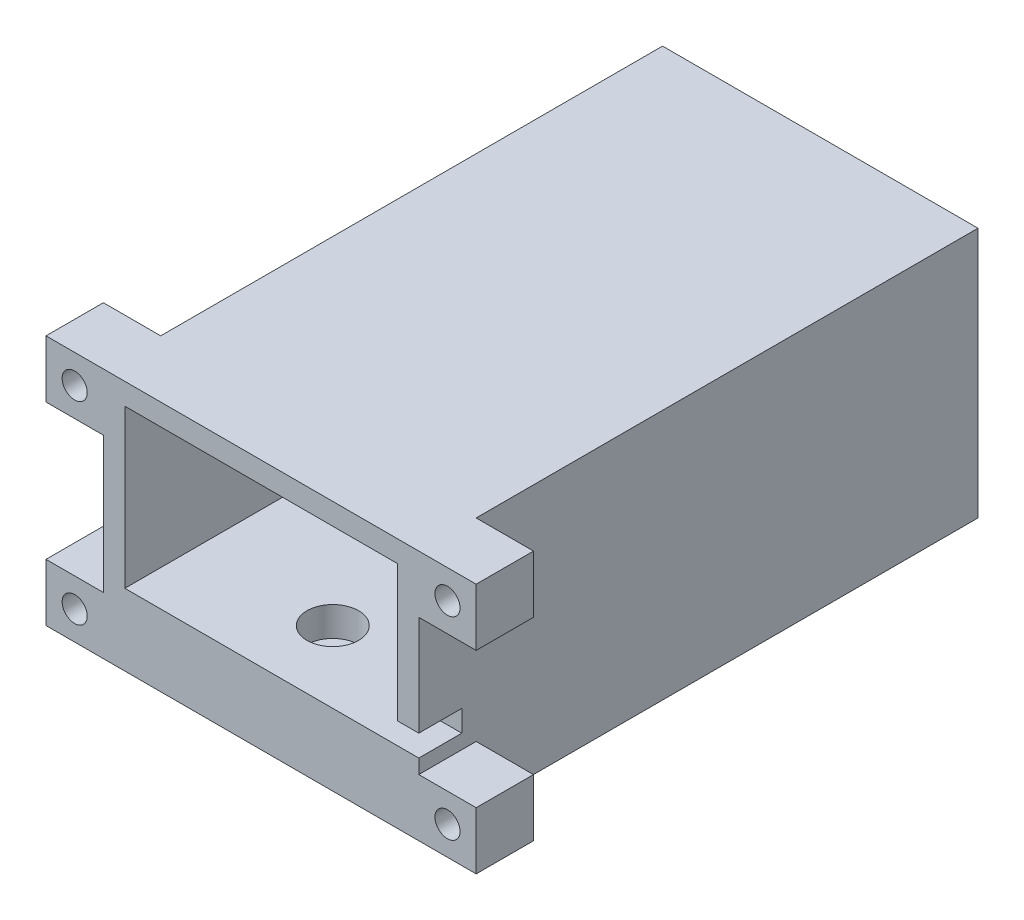
SolidWorks part; units mm, degrees
ref_plane "前基準面" through (0, 0, 0) normal (0, 0, 1) x (1, 0, 0)
ref_plane "上基準面" through (0, 0, 0) normal (0, 1, 0) x (1, 0, 0)
ref_plane "右基準面" through (0, 0, 0) normal (1, 0, 0) x (0, 0, -1)
sketch "草圖1" plane through (0, 0, 0) normal (0, 1, 0) x (1, 0, 0)
  line L1 (-22, 39) -> (22, 39)
  line L2 (-22, 39) -> (-22, -39)
  line L3 (-22, -39) -> (22, -39)
  line L4 (22, 39) -> (22, -39)
  line L5 (-22, 39) -> (22, -39) construction
  line L6 (-22, -39) -> (22, 39) construction
  point P0 (0, 0)
  dimension "D1" = 78
  dimension "D2" = 44
extrude "填料-伸長1" add sketch "草圖1" along normal blind 35
shell "薄殼1" thickness 3
sketch "草圖3" plane through (0, 10, 0) normal (0, 1, 0) x (1, 0, 0)
  line L0 (-22, -39) -> (22, -39) construction
  circle A0 centre (0, 25) radius 3.6
  circle A1 centre (0, -29) radius 3.6
  dimension "D1" = 7.2
  dimension "D2" = 54
  dimension "D3" = 10
extrude "除料-伸長1" cut sketch "草圖3" against normal blind 4.1
sketch "草圖4" plane through (0, 10, 0) normal (0, 1, 0) x (1, 0, 0)
  circle A0 centre (0, 25) radius 2.25
  circle A1 centre (0, -29) radius 2.25
  dimension "D1" = 4.5
extrude "除料-伸長2" cut sketch "草圖4" against normal up to next
sketch "草圖5" plane through (0, 0, 39) normal (0, 0, 1) x (1, 0, 0)
  line L0 (22, 35) -> (22, 0) construction
  line L1 (19, 10) -> (22, 10)
  line L2 (19, 10) -> (19, 13)
  line L3 (19, 13) -> (22, 13)
  line L4 (22, 10) -> (22, 13)
  dimension "D1" = 3
extrude "除料-伸長3" cut sketch "草圖5" against normal blind 6
sketch "草圖6" plane through (0, 0, 39) normal (0, 0, 1) x (1, 0, 0)
  line L0 (0, 0) -> (0, 15.8602) construction
  line L1 (-30, 27) -> (-22, 27)
  line L2 (-30, 27) -> (-30, 35)
  line L3 (-30, 35) -> (-22, 35)
  line L4 (-22, 27) -> (-22, 35)
  line L5 (-30, 27) -> (-22, 35) construction
  line L6 (-30, 35) -> (-22, 27) construction
  line L7 (-30, 8) -> (-22, 8)
  line L8 (-30, 8) -> (-30, 0)
  line L9 (-30, 0) -> (-22, 0)
  line L10 (-22, 8) -> (-22, 0)
  line L11 (-30, 8) -> (-22, 0) construction
  line L12 (-30, 0) -> (-22, 8) construction
  line L13 (30, 0) -> (22, 8) construction
  line L14 (30, 8) -> (22, 0) construction
  line L15 (30, 35) -> (22, 27) construction
  line L16 (30, 27) -> (22, 35) construction
  line L17 (22, 8) -> (22, 0)
  line L18 (30, 0) -> (22, 0)
  line L19 (30, 8) -> (30, 0)
  line L20 (30, 8) -> (22, 8)
  line L21 (22, 27) -> (22, 35)
  line L22 (30, 35) -> (22, 35)
  line L23 (30, 27) -> (30, 35)
  line L24 (30, 27) -> (22, 27)
  circle A0 centre (-26, 31) radius 1.75
  circle A1 centre (-26, 4) radius 1.75
  circle A2 centre (26, 31) radius 1.75
  circle A3 centre (26, 4) radius 1.75
  point P0 (-26, 31)
  point P6 (-26, 4)
  point P23 (26, 4)
  point P24 (26, 31)
  dimension "D2" = 3.5
  dimension "D1" = 8
extrude "填料-伸長2" add sketch "草圖6" against normal blind 8
sketch "草圖7" plane through (0, 0, 31) normal (0, 0, -1) x (-1, 0, 0)
  line L0 (0, 0) -> (0, 11.4673) construction
  line L1 (27.5877, 6.75) -> (29.1754, 4)
  line L2 (-22.8246, 31) -> (-24.4123, 33.75)
  line L3 (-24.4123, 33.75) -> (-27.5877, 33.75)
  line L4 (-27.5877, 33.75) -> (-29.1754, 31)
  line L5 (-29.1754, 31) -> (-27.5877, 28.25)
  line L6 (-27.5877, 28.25) -> (-24.4123, 28.25)
  line L7 (-24.4123, 28.25) -> (-22.8246, 31)
  line L8 (-29.1754, 4) -> (-27.5877, 1.25)
  line L9 (-27.5877, 1.25) -> (-24.4123, 1.25)
  line L10 (-24.4123, 1.25) -> (-22.8246, 4)
  line L11 (-22.8246, 4) -> (-24.4123, 6.75)
  line L12 (-24.4123, 6.75) -> (-27.5877, 6.75)
  line L13 (-27.5877, 6.75) -> (-29.1754, 4)
  line L14 (24.4123, 6.75) -> (27.5877, 6.75)
  line L15 (22.8246, 4) -> (24.4123, 6.75)
  line L16 (24.4123, 1.25) -> (22.8246, 4)
  line L17 (27.5877, 1.25) -> (24.4123, 1.25)
  line L18 (29.1754, 4) -> (27.5877, 1.25)
  line L19 (24.4123, 28.25) -> (22.8246, 31)
  line L20 (27.5877, 28.25) -> (24.4123, 28.25)
  line L21 (29.1754, 31) -> (27.5877, 28.25)
  line L22 (27.5877, 33.75) -> (29.1754, 31)
  line L23 (24.4123, 33.75) -> (27.5877, 33.75)
  line L24 (22.8246, 31) -> (24.4123, 33.75)
  circle A0 centre (-26, 31) radius 2.75 construction
  circle A1 centre (-26, 4) radius 2.75 construction
  circle A2 centre (26, 4) radius 2.75 construction
  circle A3 centre (26, 31) radius 2.75 construction
  dimension "D1" = 5.5
extrude "除料-伸長4" cut sketch "草圖7" against normal blind 2.6
sketch "草圖8" plane through (0, 0, -36) normal (0, 0, 1) x (1, 0, 0)
  circle A0 centre (0, 20) radius 5
  point P2 (0, 0)
  dimension "D1" = 10
  dimension "D2" = 20
extrude "除料-伸長5" cut sketch "草圖8" against normal up to next
